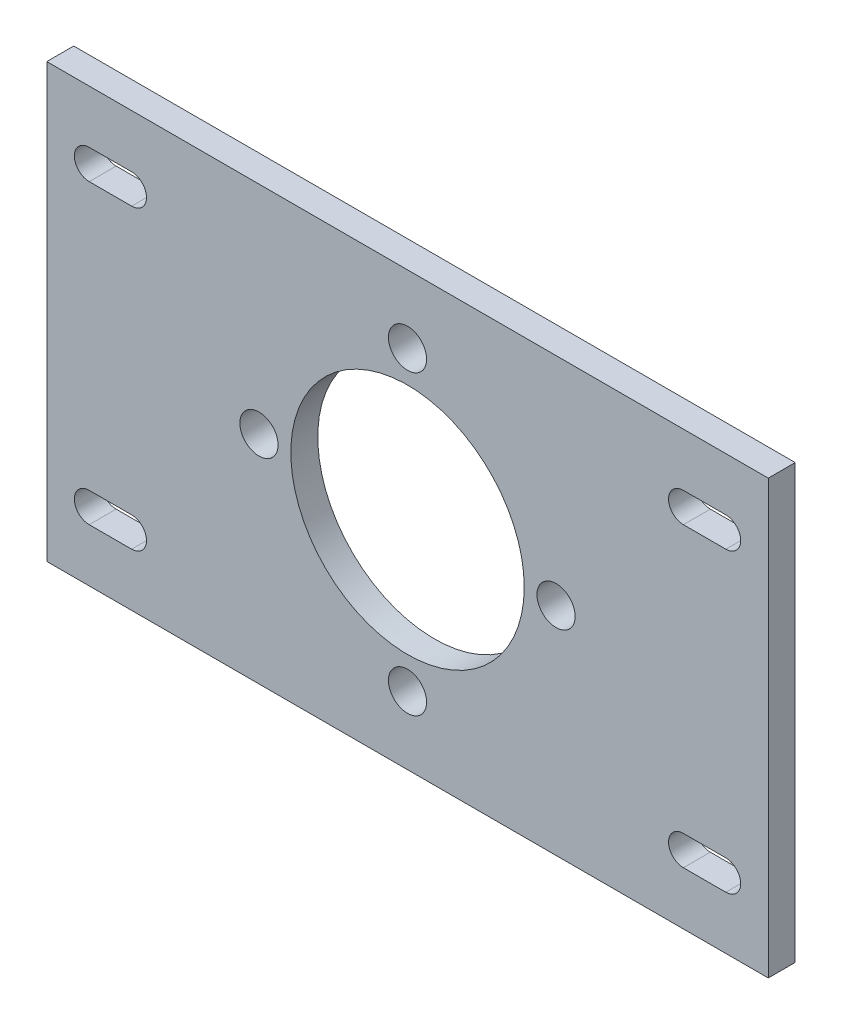
SolidWorks part; units mm, degrees
ref_plane "Front Plane" through (0, 0, 0) normal (0, 0, 1) x (1, 0, 0)
ref_plane "Top Plane" through (0, 0, 0) normal (0, 1, 0) x (1, 0, 0)
ref_plane "Right Plane" through (0, 0, 0) normal (1, 0, 0) x (0, 0, -1)
sketch "Sketch1" plane through (0, 0, 0) normal (0, 0, 1) x (1, 0, 0)
  line L0 (-42.5, 25.5) -> (42.5, -25.5) construction
  line L1 (-42.5, -25.5) -> (42.5, -25.5)
  line L2 (-42.5, -25.5) -> (-42.5, 25.5)
  line L3 (-42.5, 25.5) -> (42.5, 25.5)
  line L4 (42.5, -25.5) -> (42.5, 25.5)
  line L5 (-37.5, 17.5) -> (-32.5, 17.5) construction
  line L6 (-37.5, 19.25) -> (-32.5, 19.25)
  line L7 (-37.5, 15.75) -> (-32.5, 15.75)
  line L8 (0, -55) -> (0, 55) construction
  line L9 (37.5, 17.5) -> (32.5, 17.5) construction
  line L10 (37.5, 19.25) -> (32.5, 19.25)
  line L11 (37.5, 15.75) -> (32.5, 15.75)
  line L12 (55, 0) -> (-55, 0) construction
  line L13 (37.5, -17.5) -> (32.5, -17.5) construction
  line L14 (37.5, -19.25) -> (32.5, -19.25)
  line L15 (37.5, -15.75) -> (32.5, -15.75)
  line L16 (-37.5, -17.5) -> (-32.5, -17.5) construction
  line L17 (-37.5, -19.25) -> (-32.5, -19.25)
  line L18 (-37.5, -15.75) -> (-32.5, -15.75)
  circle A0 centre (0, 0) radius 13.75
  circle A1 centre (0, 17.5) radius 2.25
  circle A2 centre (17.5, 0) radius 2.25
  circle A3 centre (0, -17.5) radius 2.25
  circle A4 centre (-17.5, 0) radius 2.25
  circle A5 centre (0, 17.5) radius 3.5 construction
  arc A6 (-37.5, 19.25) -> (-37.5, 15.75) centre (-37.5, 17.5) ccw
  arc A7 (-32.5, 15.75) -> (-32.5, 19.25) centre (-32.5, 17.5) ccw
  arc A8 (37.5, 19.25) -> (37.5, 15.75) centre (37.5, 17.5) cw
  arc A9 (32.5, 15.75) -> (32.5, 19.25) centre (32.5, 17.5) cw
  arc A10 (37.5, -19.25) -> (37.5, -15.75) centre (37.5, -17.5) ccw
  arc A11 (32.5, -15.75) -> (32.5, -19.25) centre (32.5, -17.5) ccw
  arc A12 (-37.5, -19.25) -> (-37.5, -15.75) centre (-37.5, -17.5) cw
  arc A13 (-32.5, -15.75) -> (-32.5, -19.25) centre (-32.5, -17.5) cw
  point P18 (0, 0)
  point P19 (-35, 17.5)
  point P24 (-35.0382, 16.1752)
  point P29 (35, 17.5)
  point P38 (35, -17.5)
  point P45 (-35, -17.5)
  point P50 (0, 0)
  dimension "D2" = 27.5
  dimension "D3" = 7
  dimension "4.5" = 4.5
  dimension "D6" = 3.5
  dimension "D1" = 85
  dimension "D5" = 35
  dimension "D7" = 5
  dimension "D8" = 70
  dimension "D9" = 8
  dimension "D4" = 4
extrude "Boss-Extrude1" add sketch "Sketch1" along normal blind 3.175
